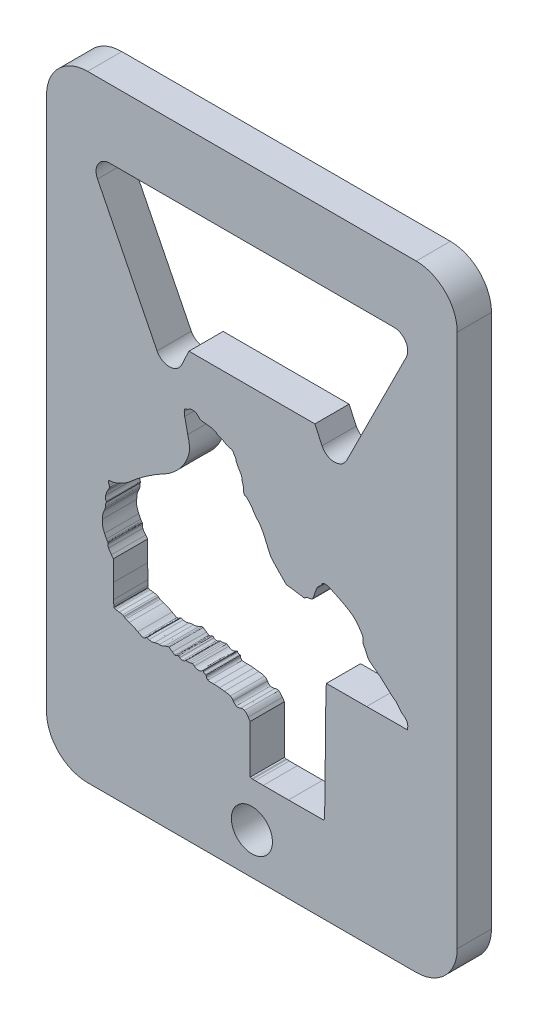
SolidWorks part; units mm, degrees
ref_plane "Front Plane" through (0, 0, 0) normal (0, 0, 1) x (1, 0, 0)
ref_plane "Top Plane" through (0, 0, 0) normal (0, 1, 0) x (1, 0, 0)
ref_plane "Right Plane" through (0, 0, 0) normal (1, 0, 0) x (0, 0, -1)
sketch "Sketch1" plane through (0, 0, 0) normal (0, 0, 1) x (1, 0, 0)
  line L0 (25.4, 0) -> (25.4, 57.15) construction
  line L1 (6.35, 28.575) -> (44.45, 28.575) construction
  line L2 (38.5851, 50.8) -> (12.2149, 50.8)
  line L3 (11.079, 48.962) -> (16.6046, 37.9107)
  line L4 (18.8914, 37.9416) -> (19.558, 39.37)
  line L5 (19.558, 39.37) -> (31.242, 39.37)
  line L6 (31.9086, 37.9416) -> (31.242, 39.37)
  line L7 (40.64, 0) -> (10.16, 0)
  line L8 (44.45, 3.81) -> (44.45, 53.34)
  line L9 (40.64, 57.15) -> (10.16, 57.15)
  line L10 (6.35, 3.81) -> (6.35, 53.34)
  line L11 (44.45, 0) -> (6.35, 57.15) construction
  line L12 (44.45, 57.15) -> (6.35, 0) construction
  line L13 (39.721, 48.962) -> (34.1954, 37.9107)
  arc A0 (18.8914, 37.9416) -> (16.6046, 37.9107) centre (17.7406, 38.4787) cw
  arc A1 (11.079, 48.962) -> (12.2149, 50.8) centre (12.2149, 49.53) cw
  arc A2 (39.721, 48.962) -> (38.5851, 50.8) centre (38.5851, 49.53) ccw
  arc A3 (31.9086, 37.9416) -> (34.1954, 37.9107) centre (33.0594, 38.4787) ccw
  arc A4 (44.45, 53.34) -> (40.64, 57.15) centre (40.64, 53.34) ccw
  arc A5 (44.45, 3.81) -> (40.64, 0) centre (40.64, 3.81) cw
  arc A6 (10.16, 0) -> (6.35, 3.81) centre (10.16, 3.81) cw
  arc A7 (10.16, 57.15) -> (6.35, 53.34) centre (10.16, 53.34) ccw
  point P6 (25.4, 28.575)
  point P11 (25.4, 50.8)
  point P13 (17.78, 35.56)
  point P16 (10.16, 50.8)
  point P24 (25.4, 39.37)
  point P25 (25.4, 28.575)
  dimension "D8" = 3.81
  dimension "D9" = 3.81
  dimension "D11" = 1.27
  dimension "D12" = 1.27
  dimension "D1" = 25.4
  dimension "D2" = 57.15
  dimension "D3" = 38.1
  dimension "D4" = 15.24
  dimension "D5" = 6.35
  dimension "D6" = 5.842
  dimension "D7" = 7.62
  dimension "D10" = 11.43
extrude "Boss-Extrude1" add sketch "Sketch1" along normal blind 3.175
sketch "Sketch3" plane through (0, 0, 3.175) normal (0, 0, 1) x (1, 0, 0)
  line L0 (25.4, 30.5609) -> (25.4, 0) construction
  line L1 (10.16, 0) -> (40.64, 0) construction
  circle A0 centre (25.4, 3.81) radius 1.905
  dimension "D1" = 3.81
  dimension "D2" = 3.81
extrude "Cut-Extrude1" cut sketch "Sketch3" against normal through all
sketch "Sketch4" plane through (0, 0, 3.175) normal (0, 0, 1) x (1, 0, 0)
  line L0 (26.4493, 7.9305) -> (26.4493, 7.9305)
  line L1 (26.4493, 7.9305) -> (26.4493, 7.9305)
  line L2 (25.0594, 12.7217) -> (25.2408, 12.4602)
  line L3 (25.2408, 12.4602) -> (25.2408, 10.2385)
  line L4 (25.2408, 10.2385) -> (25.2408, 7.9854)
  line L5 (25.2408, 7.9854) -> (25.3918, 7.9488)
  line L6 (12.3722, 19.426) -> (12.559, 19.1948)
  line L7 (12.559, 19.1948) -> (12.5599, 17.2922)
  line L8 (29.4026, 25.02) -> (28.5879, 25.1333)
  line L9 (28.5879, 25.1333) -> (27.8748, 25.8579)
  line L10 (32.2767, 18.4905) -> (32.3083, 19.0514)
  line L11 (32.3083, 19.0514) -> (36.0488, 19.066)
  line L12 (36.0488, 19.066) -> (39.8429, 19.0808)
  line L13 (39.8429, 19.0808) -> (39.8604, 19.337)
  line L14 (28.7946, 7.9325) -> (32.0832, 7.9484)
  line L15 (32.0832, 7.9484) -> (32.1298, 8.1226)
  spline S0 degree 3 poles (25.706, 7.937) (25.8875, 7.9341) (26.1415, 7.9319) (26.4493, 7.9305) knots 0 0 0 0 1 1 1 1
  spline S1 degree 3 poles (25.4902, 7.9421) (25.5427, 7.9402) (25.6152, 7.9385) (25.706, 7.937) knots 0 0 0 0 1 1 1 1
  spline S2 degree 3 poles (25.4268, 7.9449) (25.4428, 7.9438) (25.464, 7.943) (25.4902, 7.9421) knots 0 0 0 0 1 1 1 1
  spline S3 degree 3 poles (25.3918, 7.9488) (25.4019, 7.9463) (25.4108, 7.9459) (25.4268, 7.9449) knots 0 0 0 0 1 1 1 1
  spline S4 degree 3 poles (24.7149, 13.0839) (24.8186, 13.0306) (24.9247, 12.916) (25.0594, 12.7217) knots 0 0 0 0 1 1 1 1
  spline S5 degree 3 poles (24.362, 13.0862) (24.5074, 13.1342) (24.6112, 13.1372) (24.7149, 13.0839) knots 0 0 0 0 1 1 1 1
  spline S6 degree 3 poles (23.949, 13.0665) (24.0645, 13.0236) (24.2003, 13.0328) (24.362, 13.0862) knots 0 0 0 0 1 1 1 1
  spline S7 degree 3 poles (23.6661, 13.3456) (23.7418, 13.2036) (23.8334, 13.1095) (23.949, 13.0665) knots 0 0 0 0 1 1 1 1
  spline S8 degree 3 poles (23.4001, 13.5896) (23.5264, 13.5348) (23.606, 13.4584) (23.6661, 13.3456) knots 0 0 0 0 1 1 1 1
  spline S9 degree 3 poles (22.8576, 13.6917) (23.1001, 13.6761) (23.2739, 13.6444) (23.4001, 13.5896) knots 0 0 0 0 1 1 1 1
  spline S10 degree 3 poles (22.3946, 13.7502) (22.5077, 13.727) (22.7138, 13.701) (22.8576, 13.6917) knots 0 0 0 0 1 1 1 1
  spline S11 degree 3 poles (21.8186, 13.777) (22.0267, 13.7846) (22.2909, 13.7715) (22.3946, 13.7502) knots 0 0 0 0 1 1 1 1
  spline S12 degree 3 poles (21.328, 13.826) (21.4354, 13.7818) (21.5937, 13.7688) (21.8186, 13.777) knots 0 0 0 0 1 1 1 1
  spline S13 degree 3 poles (21.1665, 14.0617) (21.1665, 13.9532) (21.2207, 13.8702) (21.328, 13.826) knots 0 0 0 0 1 1 1 1
  spline S14 degree 3 poles (21.1468, 14.1534) (21.1584, 14.1397) (21.1665, 14.1115) (21.1665, 14.0617) knots 0 0 0 0 1 1 1 1
  spline S15 degree 3 poles (21.0751, 14.1744) (21.1159, 14.1744) (21.1352, 14.167) (21.1468, 14.1534) knots 0 0 0 0 1 1 1 1
  spline S16 degree 3 poles (20.8974, 14.3098) (20.9184, 14.2296) (20.9912, 14.1744) (21.0751, 14.1744) knots 0 0 0 0 1 1 1 1
  spline S17 degree 3 poles (20.8796, 14.369) (20.8842, 14.359) (20.89, 14.3382) (20.8974, 14.3098) knots 0 0 0 0 1 1 1 1
  spline S18 degree 3 poles (20.8781, 14.3719) (20.8787, 14.3709) (20.8786, 14.3713) (20.8796, 14.369) knots 0 0 0 0 1 1 1 1
  spline S19 degree 3 poles (20.8508, 14.3572) (20.8683, 14.3692) (20.8771, 14.3713) (20.8781, 14.3719) knots 0 0 0 0 1 1 1 1
  spline S20 degree 3 poles (20.7684, 14.2945) (20.8045, 14.3228) (20.8315, 14.344) (20.8508, 14.3572) knots 0 0 0 0 1 1 1 1
  spline S21 degree 3 poles (20.0661, 14.3223) (20.2983, 14.1451) (20.5633, 14.1331) (20.7684, 14.2945) knots 0 0 0 0 1 1 1 1
  spline S22 degree 3 poles (19.8863, 14.4255) (19.9348, 14.4157) (19.9836, 14.3851) (20.0661, 14.3223) knots 0 0 0 0 1 1 1 1
  spline S23 degree 3 poles (19.6858, 14.3987) (19.7829, 14.4255) (19.8378, 14.4352) (19.8863, 14.4255) knots 0 0 0 0 1 1 1 1
  spline S24 degree 3 poles (19.4952, 14.3632) (19.5558, 14.3693) (19.6237, 14.3815) (19.6858, 14.3987) knots 0 0 0 0 1 1 1 1
  spline S25 degree 3 poles (19.3464, 14.3656) (19.3833, 14.356) (19.4348, 14.357) (19.4952, 14.3632) knots 0 0 0 0 1 1 1 1
  spline S26 degree 3 poles (19.204, 14.3224) (19.2311, 14.3551) (19.3017, 14.3773) (19.3464, 14.3656) knots 0 0 0 0 1 1 1 1
  spline S27 degree 3 poles (18.9552, 14.2346) (19.0521, 14.2334) (19.1504, 14.2579) (19.204, 14.3224) knots 0 0 0 0 1 1 1 1
  spline S28 degree 3 poles (18.7057, 14.3283) (18.7598, 14.2631) (18.8582, 14.2359) (18.9552, 14.2346) knots 0 0 0 0 1 1 1 1
  spline S29 degree 3 poles (18.5788, 14.4002) (18.6264, 14.3977) (18.6662, 14.3759) (18.7057, 14.3283) knots 0 0 0 0 1 1 1 1
  spline S30 degree 3 poles (18.4025, 14.3401) (18.473, 14.3841) (18.5312, 14.4026) (18.5788, 14.4002) knots 0 0 0 0 1 1 1 1
  spline S31 degree 3 poles (18.2463, 14.3123) (18.3036, 14.2957) (18.3533, 14.3094) (18.4025, 14.3401) knots 0 0 0 0 1 1 1 1
  spline S32 degree 3 poles (18.0241, 14.4414) (18.1243, 14.3701) (18.1889, 14.3289) (18.2463, 14.3123) knots 0 0 0 0 1 1 1 1
  spline S33 degree 3 poles (17.7109, 14.6629) (17.7524, 14.6341) (17.8938, 14.5342) (18.0241, 14.4414) knots 0 0 0 0 1 1 1 1
  spline S34 degree 3 poles (17.5939, 14.6591) (17.659, 14.6757) (17.6985, 14.6714) (17.7109, 14.6629) knots 0 0 0 0 1 1 1 1
  spline S35 degree 3 poles (17.3291, 14.5553) (17.4402, 14.6078) (17.5288, 14.6424) (17.5939, 14.6591) knots 0 0 0 0 1 1 1 1
  spline S36 degree 3 poles (16.8035, 14.4229) (16.932, 14.4023) (17.1021, 14.4478) (17.3291, 14.5553) knots 0 0 0 0 1 1 1 1
  spline S37 degree 3 poles (16.3764, 14.3603) (16.5185, 14.4093) (16.719, 14.4365) (16.8035, 14.4229) knots 0 0 0 0 1 1 1 1
  spline S38 degree 3 poles (15.8561, 14.3459) (16.0623, 14.2779) (16.1439, 14.28) (16.3764, 14.3603) knots 0 0 0 0 1 1 1 1
  spline S39 degree 3 poles (15.6529, 14.3932) (15.6924, 14.3952) (15.7524, 14.3801) (15.8561, 14.3459) knots 0 0 0 0 1 1 1 1
  spline S40 degree 3 poles (15.5436, 14.3345) (15.5888, 14.3754) (15.6134, 14.3912) (15.6529, 14.3932) knots 0 0 0 0 1 1 1 1
  spline S41 degree 3 poles (15.2761, 14.2463) (15.3836, 14.2262) (15.4633, 14.2618) (15.5436, 14.3345) knots 0 0 0 0 1 1 1 1
  spline S42 degree 3 poles (14.8213, 14.4593) (15.0343, 14.335) (15.1687, 14.2663) (15.2761, 14.2463) knots 0 0 0 0 1 1 1 1
  spline S43 degree 3 poles (14.0272, 14.807) (14.2532, 14.7384) (14.6137, 14.5805) (14.8213, 14.4593) knots 0 0 0 0 1 1 1 1
  spline S44 degree 3 poles (13.7096, 14.9277) (13.7954, 14.8863) (13.9067, 14.8436) (14.0272, 14.807) knots 0 0 0 0 1 1 1 1
  spline S45 degree 3 poles (13.6015, 14.9881) (13.6302, 14.9686) (13.6667, 14.9484) (13.7096, 14.9277) knots 0 0 0 0 1 1 1 1
  spline S46 degree 3 poles (13.5394, 15.0479) (13.5516, 15.025) (13.5728, 15.0076) (13.6015, 14.9881) knots 0 0 0 0 1 1 1 1
  spline S47 degree 3 poles (13.423, 15.1207) (13.493, 15.1) (13.524, 15.0765) (13.5394, 15.0479) knots 0 0 0 0 1 1 1 1
  spline S48 degree 3 poles (13.0922, 15.1718) (13.2467, 15.1574) (13.353, 15.1414) (13.423, 15.1207) knots 0 0 0 0 1 1 1 1
  spline S49 degree 3 poles (12.7813, 15.2204) (12.8665, 15.2003) (12.9765, 15.1826) (13.0922, 15.1718) knots 0 0 0 0 1 1 1 1
  spline S50 degree 3 poles (12.6738, 15.2523) (12.7023, 15.2411) (12.7387, 15.2305) (12.7813, 15.2204) knots 0 0 0 0 1 1 1 1
  spline S51 degree 3 poles (12.6099, 15.294) (12.6244, 15.2712) (12.6453, 15.2634) (12.6738, 15.2523) knots 0 0 0 0 1 1 1 1
  spline S52 degree 3 poles (12.6013, 15.3217) (12.603, 15.3116) (12.6019, 15.3066) (12.6099, 15.294) knots 0 0 0 0 1 1 1 1
  spline S53 degree 3 poles (12.5966, 15.3596) (12.5981, 15.3442) (12.5996, 15.3317) (12.6013, 15.3217) knots 0 0 0 0 1 1 1 1
  spline S54 degree 3 poles (12.5881, 15.4861) (12.5908, 15.4331) (12.5936, 15.3906) (12.5966, 15.3596) knots 0 0 0 0 1 1 1 1
  spline S55 degree 3 poles (12.5737, 15.9201) (12.5778, 15.7403) (12.5827, 15.5921) (12.5881, 15.4861) knots 0 0 0 0 1 1 1 1
  spline S56 degree 3 poles (12.5599, 17.2922) (12.5602, 16.766) (12.5655, 16.2799) (12.5737, 15.9201) knots 0 0 0 0 1 1 1 1
  spline S57 degree 3 poles (12.1014, 19.8248) (12.1497, 19.7177) (12.236, 19.5946) (12.3722, 19.426) knots 0 0 0 0 1 1 1 1
  spline S58 degree 3 poles (12.0637, 20.1211) (12.0443, 20.0242) (12.0531, 19.9319) (12.1014, 19.8248) knots 0 0 0 0 1 1 1 1
  spline S59 degree 3 poles (12.0683, 20.2352) (12.0741, 20.2094) (12.0735, 20.1702) (12.0637, 20.1211) knots 0 0 0 0 1 1 1 1
  spline S60 degree 3 poles (12.039, 20.2772) (12.0531, 20.2718) (12.0624, 20.2611) (12.0683, 20.2352) knots 0 0 0 0 1 1 1 1
  spline S61 degree 3 poles (12.0085, 20.3009) (12.0176, 20.2908) (12.0249, 20.2827) (12.039, 20.2772) knots 0 0 0 0 1 1 1 1
  spline S62 degree 3 poles (11.9796, 20.3387) (11.99, 20.3235) (11.9995, 20.311) (12.0085, 20.3009) knots 0 0 0 0 1 1 1 1
  spline S63 degree 3 poles (11.9079, 20.4584) (11.9345, 20.4096) (11.9588, 20.369) (11.9796, 20.3387) knots 0 0 0 0 1 1 1 1
  spline S64 degree 3 poles (11.732, 20.8249) (11.7918, 20.6856) (11.8546, 20.5559) (11.9079, 20.4584) knots 0 0 0 0 1 1 1 1
  spline S65 degree 3 poles (11.538, 21.8613) (11.5144, 21.3609) (11.524, 21.3091) (11.732, 20.8249) knots 0 0 0 0 1 1 1 1
  spline S66 degree 3 poles (11.7164, 22.6865) (11.5941, 22.4486) (11.5578, 22.2801) (11.538, 21.8613) knots 0 0 0 0 1 1 1 1
  spline S67 degree 3 poles (11.8134, 22.9242) (11.7926, 22.8531) (11.7587, 22.7687) (11.7164, 22.6865) knots 0 0 0 0 1 1 1 1
  spline S68 degree 3 poles (11.8343, 23.0763) (11.8398, 23.0554) (11.8343, 22.9953) (11.8134, 22.9242) knots 0 0 0 0 1 1 1 1
  spline S69 degree 3 poles (11.8727, 23.3385) (11.8318, 23.2621) (11.8144, 23.1527) (11.8343, 23.0763) knots 0 0 0 0 1 1 1 1
  spline S70 degree 3 poles (11.907, 23.4401) (11.9073, 23.4158) (11.8971, 23.3841) (11.8727, 23.3385) knots 0 0 0 0 1 1 1 1
  spline S71 degree 3 poles (11.8737, 23.5138) (11.8976, 23.4849) (11.9067, 23.4643) (11.907, 23.4401) knots 0 0 0 0 1 1 1 1
  spline S72 degree 3 poles (11.8363, 23.9172) (11.803, 23.7459) (11.8051, 23.5965) (11.8737, 23.5138) knots 0 0 0 0 1 1 1 1
  spline S73 degree 3 poles (12.0467, 24.4498) (11.9428, 24.2825) (11.8695, 24.0885) (11.8363, 23.9172) knots 0 0 0 0 1 1 1 1
  spline S74 degree 3 poles (12.1874, 24.7196) (12.1722, 24.6604) (12.1291, 24.5823) (12.0467, 24.4498) knots 0 0 0 0 1 1 1 1
  spline S75 degree 3 poles (12.1655, 24.8993) (12.1934, 24.8222) (12.2026, 24.7789) (12.1874, 24.7196) knots 0 0 0 0 1 1 1 1
  spline S76 degree 3 poles (12.1056, 25.0968) (12.1157, 25.0442) (12.1363, 24.9801) (12.1655, 24.8993) knots 0 0 0 0 1 1 1 1
  spline S77 degree 3 poles (12.1134, 25.2272) (12.0951, 25.1921) (12.0955, 25.1494) (12.1056, 25.0968) knots 0 0 0 0 1 1 1 1
  spline S78 degree 3 poles (12.2124, 25.2936) (12.1677, 25.283) (12.1317, 25.2624) (12.1134, 25.2272) knots 0 0 0 0 1 1 1 1
  spline S79 degree 3 poles (12.3849, 25.3068) (12.3132, 25.3068) (12.2571, 25.3041) (12.2124, 25.2936) knots 0 0 0 0 1 1 1 1
  spline S80 degree 3 poles (13.2242, 25.5925) (12.8882, 25.426) (12.5517, 25.3068) (12.3849, 25.3068) knots 0 0 0 0 1 1 1 1
  spline S81 degree 3 poles (14.0886, 26.1529) (13.9001, 25.9724) (13.5602, 25.759) (13.2242, 25.5925) knots 0 0 0 0 1 1 1 1
  spline S82 degree 3 poles (17.2516, 28.3583) (16.3205, 27.8858) (14.768, 26.8036) (14.0886, 26.1529) knots 0 0 0 0 1 1 1 1
  spline S83 degree 3 poles (19.146, 30.1326) (18.7706, 29.4612) (17.9979, 28.7371) (17.2516, 28.3583) knots 0 0 0 0 1 1 1 1
  spline S84 degree 3 poles (19.4524, 32.6197) (19.7238, 31.5446) (19.664, 31.0589) (19.146, 30.1326) knots 0 0 0 0 1 1 1 1
  spline S85 degree 3 poles (19.1661, 33.9288) (19.2162, 33.6147) (19.3121, 33.1758) (19.4524, 32.6197) knots 0 0 0 0 1 1 1 1
  spline S86 degree 3 poles (19.1256, 34.3061) (19.1275, 34.2116) (19.1411, 34.0858) (19.1661, 33.9288) knots 0 0 0 0 1 1 1 1
  spline S87 degree 3 poles (19.1619, 34.5031) (19.1293, 34.4637) (19.1238, 34.4007) (19.1256, 34.3061) knots 0 0 0 0 1 1 1 1
  spline S88 degree 3 poles (19.3472, 34.6029) (19.2826, 34.6029) (19.2087, 34.5594) (19.1619, 34.5031) knots 0 0 0 0 1 1 1 1
  spline S89 degree 3 poles (19.4264, 34.6262) (19.395, 34.6113) (19.3638, 34.6029) (19.3472, 34.6029) knots 0 0 0 0 1 1 1 1
  spline S90 degree 3 poles (19.5146, 34.6841) (19.4904, 34.6621) (19.4579, 34.6411) (19.4264, 34.6262) knots 0 0 0 0 1 1 1 1
  spline S91 degree 3 poles (19.8409, 34.8082) (19.7151, 34.7976) (19.5951, 34.7569) (19.5146, 34.6841) knots 0 0 0 0 1 1 1 1
  spline S92 degree 3 poles (20.2044, 34.744) (20.0988, 34.7994) (19.9667, 34.8189) (19.8409, 34.8082) knots 0 0 0 0 1 1 1 1
  spline S93 degree 3 poles (20.5101, 34.495) (20.4377, 34.583) (20.3045, 34.6915) (20.2044, 34.744) knots 0 0 0 0 1 1 1 1
  spline S94 degree 3 poles (20.6892, 34.3704) (20.6007, 34.3948) (20.5661, 34.4269) (20.5101, 34.495) knots 0 0 0 0 1 1 1 1
  spline S95 degree 3 poles (21.1795, 34.3145) (20.921, 34.3325) (20.7777, 34.3459) (20.6892, 34.3704) knots 0 0 0 0 1 1 1 1
  spline S96 degree 3 poles (22.1848, 33.9998) (22.0284, 34.1882) (21.7342, 34.2761) (21.1795, 34.3145) knots 0 0 0 0 1 1 1 1
  spline S97 degree 3 poles (22.2805, 33.9377) (22.235, 33.9585) (22.1982, 33.9837) (22.1848, 33.9998) knots 0 0 0 0 1 1 1 1
  spline S98 degree 3 poles (22.4305, 33.8897) (22.3802, 33.8991) (22.3259, 33.917) (22.2805, 33.9377) knots 0 0 0 0 1 1 1 1
  spline S99 degree 3 poles (22.8471, 33.7046) (22.7262, 33.7867) (22.5448, 33.8682) (22.4305, 33.8897) knots 0 0 0 0 1 1 1 1
  spline S100 degree 3 poles (23.3388, 33.4978) (23.1849, 33.5334) (22.9588, 33.6289) (22.8471, 33.7046) knots 0 0 0 0 1 1 1 1
  spline S101 degree 3 poles (23.5985, 33.4052) (23.54, 33.4454) (23.4616, 33.4695) (23.3388, 33.4978) knots 0 0 0 0 1 1 1 1
  spline S102 degree 3 poles (23.7248, 33.2291) (23.6913, 33.3092) (23.657, 33.3649) (23.5985, 33.4052) knots 0 0 0 0 1 1 1 1
  spline S103 degree 3 poles (23.7926, 33.0926) (23.7702, 33.1305) (23.7456, 33.1794) (23.7248, 33.2291) knots 0 0 0 0 1 1 1 1
  spline S104 degree 3 poles (23.8236, 33.0456) (23.8145, 33.0575) (23.8038, 33.0736) (23.7926, 33.0926) knots 0 0 0 0 1 1 1 1
  spline S105 degree 3 poles (23.8416, 33.0259) (23.8411, 33.0262) (23.8326, 33.0337) (23.8236, 33.0456) knots 0 0 0 0 1 1 1 1
  spline S106 degree 3 poles (23.8743, 32.9857) (23.8654, 33.0024) (23.8578, 33.0158) (23.8416, 33.0259) knots 0 0 0 0 1 1 1 1
  spline S107 degree 3 poles (23.8997, 32.9249) (23.8916, 32.9484) (23.8832, 32.9689) (23.8743, 32.9857) knots 0 0 0 0 1 1 1 1
  spline S108 degree 3 poles (23.9402, 32.7578) (23.9304, 32.819) (23.9158, 32.878) (23.8997, 32.9249) knots 0 0 0 0 1 1 1 1
  spline S109 degree 3 poles (24.0385, 32.4964) (23.9857, 32.6062) (23.9487, 32.705) (23.9402, 32.7578) knots 0 0 0 0 1 1 1 1
  spline S110 degree 3 poles (24.2303, 32.1567) (24.1597, 32.2643) (24.0913, 32.3867) (24.0385, 32.4964) knots 0 0 0 0 1 1 1 1
  spline S111 degree 3 poles (24.4948, 31.4992) (24.4948, 31.7001) (24.4374, 31.8414) (24.2303, 32.1567) knots 0 0 0 0 1 1 1 1
  spline S112 degree 3 poles (24.5111, 31.3205) (24.5012, 31.3692) (24.4948, 31.4333) (24.4948, 31.4992) knots 0 0 0 0 1 1 1 1
  spline S113 degree 3 poles (24.5277, 31.2615) (24.5219, 31.2757) (24.5161, 31.2962) (24.5111, 31.3205) knots 0 0 0 0 1 1 1 1
  spline S114 degree 3 poles (24.5386, 31.2417) (24.5411, 31.2402) (24.5336, 31.2472) (24.5277, 31.2615) knots 0 0 0 0 1 1 1 1
  spline S115 degree 3 poles (24.5731, 31.1858) (24.5655, 31.2095) (24.5606, 31.2281) (24.5386, 31.2417) knots 0 0 0 0 1 1 1 1
  spline S116 degree 3 poles (24.5924, 31.0977) (24.5871, 31.1324) (24.5807, 31.1622) (24.5731, 31.1858) knots 0 0 0 0 1 1 1 1
  spline S117 degree 3 poles (24.6095, 30.8451) (24.6095, 30.9391) (24.6031, 31.0283) (24.5924, 31.0977) knots 0 0 0 0 1 1 1 1
  spline S118 degree 3 poles (24.6687, 30.4778) (24.6316, 30.5612) (24.6095, 30.6873) (24.6095, 30.8451) knots 0 0 0 0 1 1 1 1
  spline S119 degree 3 poles (24.8114, 30.3566) (24.7531, 30.3566) (24.7059, 30.3945) (24.6687, 30.4778) knots 0 0 0 0 1 1 1 1
  spline S120 degree 3 poles (24.8779, 30.3286) (24.8546, 30.3447) (24.8364, 30.3566) (24.8114, 30.3566) knots 0 0 0 0 1 1 1 1
  spline S121 degree 3 poles (24.9568, 30.2631) (24.9275, 30.2904) (24.9011, 30.3126) (24.8779, 30.3286) knots 0 0 0 0 1 1 1 1
  spline S122 degree 3 poles (25.1574, 30.0493) (25.0853, 30.1336) (25.0154, 30.2085) (24.9568, 30.2631) knots 0 0 0 0 1 1 1 1
  spline S123 degree 3 poles (25.5381, 29.5216) (25.4542, 29.6754) (25.3016, 29.8808) (25.1574, 30.0493) knots 0 0 0 0 1 1 1 1
  spline S124 degree 3 poles (25.9771, 28.942) (25.8253, 29.0973) (25.6254, 29.3615) (25.5381, 29.5216) knots 0 0 0 0 1 1 1 1
  spline S125 degree 3 poles (27.0233, 26.9243) (26.5868, 28.0156) (26.2575, 28.6554) (25.9771, 28.942) knots 0 0 0 0 1 1 1 1
  spline S126 degree 3 poles (27.8748, 25.8579) (27.2772, 26.4651) (27.1362, 26.6422) (27.0233, 26.9243) knots 0 0 0 0 1 1 1 1
  spline S127 degree 3 poles (29.9942, 24.9305) (29.8392, 24.9565) (29.6296, 24.9884) (29.4026, 25.02) knots 0 0 0 0 1 1 1 1
  spline S128 degree 3 poles (30.1813, 24.8966) (30.1355, 24.906) (30.0717, 24.9174) (29.9942, 24.9305) knots 0 0 0 0 1 1 1 1
  spline S129 degree 3 poles (30.2365, 24.8842) (30.2227, 24.8878) (30.2043, 24.8919) (30.1813, 24.8966) knots 0 0 0 0 1 1 1 1
  spline S130 degree 3 poles (30.2542, 24.8789) (30.2491, 24.8807) (30.2434, 24.8824) (30.2365, 24.8842) knots 0 0 0 0 1 1 1 1
  spline S131 degree 3 poles (30.2624, 24.8742) (30.26, 24.8751) (30.2565, 24.8781) (30.2542, 24.8789) knots 0 0 0 0 1 1 1 1
  spline S132 degree 3 poles (30.2766, 24.8826) (30.2697, 24.8773) (30.2646, 24.875) (30.2624, 24.8742) knots 0 0 0 0 1 1 1 1
  spline S133 degree 3 poles (30.3321, 24.9439) (30.3127, 24.9163) (30.2919, 24.8942) (30.2766, 24.8826) knots 0 0 0 0 1 1 1 1
  spline S134 degree 3 poles (30.7358, 25.1021) (30.528, 25.0761) (30.3919, 25.0293) (30.3321, 24.9439) knots 0 0 0 0 1 1 1 1
  spline S135 degree 3 poles (30.9945, 25.1594) (30.9523, 25.1342) (30.8764, 25.1196) (30.7358, 25.1021) knots 0 0 0 0 1 1 1 1
  spline S136 degree 3 poles (31.0826, 25.3047) (31.0546, 25.222) (31.0366, 25.1847) (30.9945, 25.1594) knots 0 0 0 0 1 1 1 1
  spline S137 degree 3 poles (31.4191, 26.232) (31.3421, 26.0665) (31.2493, 25.7988) (31.0826, 25.3047) knots 0 0 0 0 1 1 1 1
  spline S138 degree 3 poles (31.6594, 26.5378) (31.5605, 26.4623) (31.4961, 26.3975) (31.4191, 26.232) knots 0 0 0 0 1 1 1 1
  spline S139 degree 3 poles (31.8111, 26.6814) (31.7668, 26.6304) (31.7122, 26.578) (31.6594, 26.5378) knots 0 0 0 0 1 1 1 1
  spline S140 degree 3 poles (31.9013, 26.8147) (31.8894, 26.7833) (31.8553, 26.7325) (31.8111, 26.6814) knots 0 0 0 0 1 1 1 1
  spline S141 degree 3 poles (32.0046, 26.943) (31.9532, 26.9195) (31.9244, 26.8754) (31.9013, 26.8147) knots 0 0 0 0 1 1 1 1
  spline S142 degree 3 poles (32.229, 26.9709) (32.1232, 26.9709) (32.056, 26.9666) (32.0046, 26.943) knots 0 0 0 0 1 1 1 1
  spline S143 degree 3 poles (33.4266, 26.5057) (32.6912, 26.8688) (32.4338, 26.9709) (32.229, 26.9709) knots 0 0 0 0 1 1 1 1
  spline S144 degree 3 poles (35.4382, 24.9414) (35.0297, 25.5933) (34.6023, 25.9252) (33.4266, 26.5057) knots 0 0 0 0 1 1 1 1
  spline S145 degree 3 poles (35.682, 24.5041) (35.6442, 24.6059) (35.5706, 24.7302) (35.4382, 24.9414) knots 0 0 0 0 1 1 1 1
  spline S146 degree 3 poles (35.7044, 24.2151) (35.7192, 24.3231) (35.7197, 24.4023) (35.682, 24.5041) knots 0 0 0 0 1 1 1 1
  spline S147 degree 3 poles (35.7099, 23.9823) (35.6904, 24.0522) (35.691, 24.1175) (35.7044, 24.2151) knots 0 0 0 0 1 1 1 1
  spline S148 degree 3 poles (35.8429, 23.721) (35.7701, 23.8358) (35.7293, 23.9124) (35.7099, 23.9823) knots 0 0 0 0 1 1 1 1
  spline S149 degree 3 poles (36.0597, 23.2551) (36.0369, 23.3638) (35.9409, 23.5665) (35.8429, 23.721) knots 0 0 0 0 1 1 1 1
  spline S150 degree 3 poles (36.8479, 22.443) (36.362, 22.7599) (36.1068, 23.0303) (36.0597, 23.2551) knots 0 0 0 0 1 1 1 1
  spline S151 degree 3 poles (37.8564, 21.5937) (37.5238, 21.9161) (37.0732, 22.2961) (36.8479, 22.443) knots 0 0 0 0 1 1 1 1
  spline S152 degree 3 poles (38.3361, 21.1541) (38.1932, 21.2769) (38.0217, 21.4335) (37.8564, 21.5937) knots 0 0 0 0 1 1 1 1
  spline S153 degree 3 poles (38.6406, 20.9187) (38.5969, 20.9409) (38.4789, 21.0314) (38.3361, 21.1541) knots 0 0 0 0 1 1 1 1
  spline S154 degree 3 poles (39.0179, 20.5239) (38.9152, 20.6909) (38.7581, 20.8589) (38.6406, 20.9187) knots 0 0 0 0 1 1 1 1
  spline S155 degree 3 poles (39.4105, 20.1033) (39.2946, 20.1765) (39.1127, 20.37) (39.0179, 20.5239) knots 0 0 0 0 1 1 1 1
  spline S156 degree 3 poles (39.8604, 19.337) (39.8809, 19.6373) (39.7199, 19.908) (39.4105, 20.1033) knots 0 0 0 0 1 1 1 1
  spline S157 degree 3 poles (32.2428, 16.6636) (32.2553, 17.642) (32.2678, 18.332) (32.2767, 18.4905) knots 0 0 0 0 1 1 1 1
  spline S158 degree 3 poles (32.2077, 13.0935) (32.2176, 14.4163) (32.2302, 15.6851) (32.2428, 16.6636) knots 0 0 0 0 1 1 1 1
  spline S159 degree 3 poles (32.1703, 9.6508) (32.1842, 10.5506) (32.1978, 11.7704) (32.2077, 13.0935) knots 0 0 0 0 1 1 1 1
  spline S160 degree 3 poles (32.1495, 8.5683) (32.1562, 8.8311) (32.1633, 9.2009) (32.1703, 9.6508) knots 0 0 0 0 1 1 1 1
  spline S161 degree 3 poles (32.1397, 8.2578) (32.1428, 8.3324) (32.1462, 8.437) (32.1495, 8.5683) knots 0 0 0 0 1 1 1 1
  spline S162 degree 3 poles (32.1351, 8.1686) (32.1366, 8.1906) (32.1381, 8.2205) (32.1397, 8.2578) knots 0 0 0 0 1 1 1 1
  spline S163 degree 3 poles (32.1298, 8.1226) (32.1331, 8.1351) (32.1335, 8.1465) (32.1351, 8.1686) knots 0 0 0 0 1 1 1 1
  spline S164 degree 3 poles (26.4493, 7.9305) (27.0649, 7.9277) (27.8962, 7.9282) (28.7946, 7.9325) knots 0 0 0 0 1 1 1 1
extrude "Cut-Extrude3" cut sketch "Sketch4" against normal through all contours S0 S164 L14 L15 S163 S162 S161 S160 S159 S158 S157 L10 L11 L12 L13 S156 S155 S154 S153 S152 S151 S150 S149 S148 S147 S146 S145 S144 S143 S142 S141 S140 S139 S138 S137 S136 S135 S134 S133 S132 S131 S130 S129 S128 S127 L8 L9 S126 S125 S124 S123
